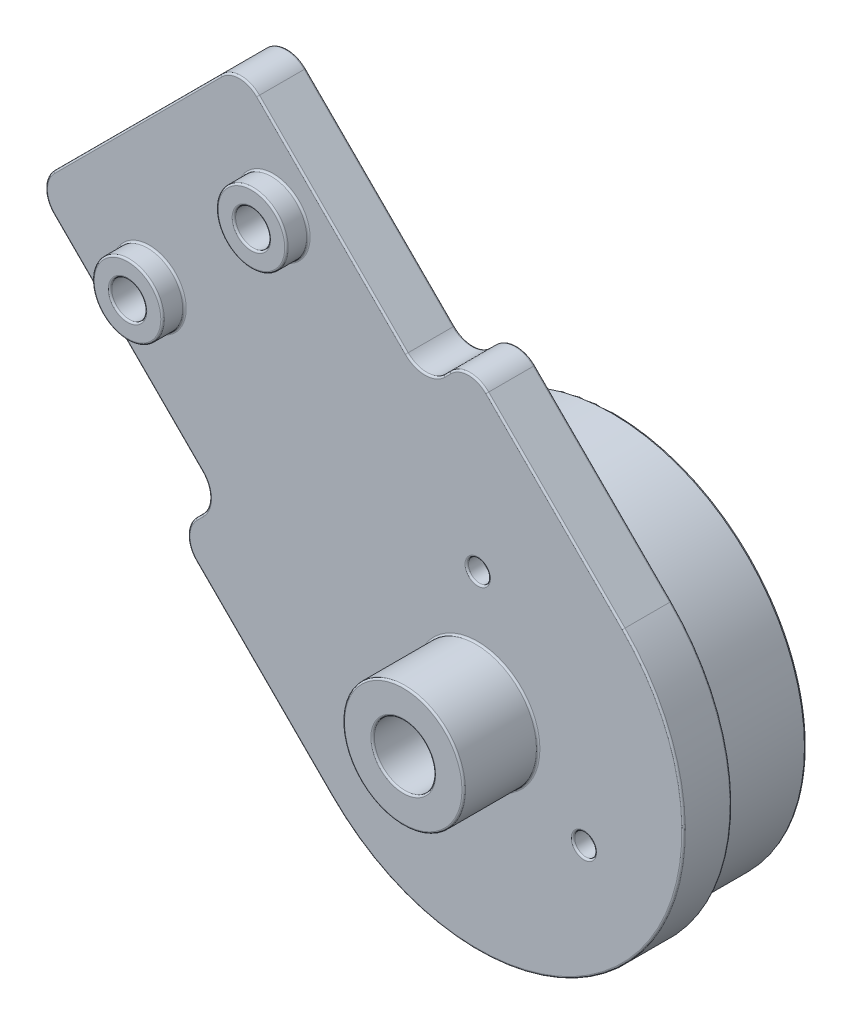
SolidWorks part; units mm, degrees
ref_plane "Front Plane" through (0, 0, 0) normal (0, 0, 1) x (1, 0, 0)
ref_plane "Top Plane" through (0, 0, 0) normal (0, 1, 0) x (1, 0, 0)
ref_plane "Right Plane" through (0, 0, 0) normal (1, 0, 0) x (0, 0, -1)
sketch "Sketch1" plane through (0, 0, 0) normal (0, 0, 1) x (1, 0, 0)
  line L0 (-100, 0) -> (100, 0) construction
  line L1 (-100, 0) -> (0, 100) construction
  line L2 (0, 100) -> (100, 0) construction
  line L3 (0, 0) -> (-50, 50) construction
  line L4 (-40, 60) -> (40, 60) construction
  line L5 (0, 100) -> (0, 60) construction
  line L6 (-56.5165, 43.4835) -> (-40, 60)
  line L7 (-40, 60) -> (40, 60)
  line L8 (40, 60) -> (86.565, 13.435) construction
  line L9 (-49.4454, 36.4124) -> (-35.8579, 50)
  line L10 (-35.8579, 50) -> (35.8579, 50)
  line L11 (35.8579, 50) -> (79.4939, 6.364)
  line L12 (-63.5876, 50.5546) -> (-44.1421, 70)
  line L13 (-44.1421, 70) -> (44.1421, 70)
  line L14 (44.1421, 70) -> (93.636, 20.5061)
  line L15 (-63.5876, 50.5546) -> (-49.4454, 36.4124)
  line L16 (93.636, 20.5061) -> (79.4939, 6.364)
  line L17 (91.1612, 18.0312) -> (104.5962, 4.5962)
  line L18 (81.9688, 8.8388) -> (95.4038, -4.5962)
  line L19 (90.1005, 24.0416) -> (75.9584, 9.8995) construction
  line L20 (6, 70) -> (3.4304, 82.6944)
  line L21 (-6, 70) -> (-3.4304, 82.6944)
  line L22 (40, 60) -> (86.565, 13.435)
  circle A0 centre (-100, 0) radius 20
  circle A1 centre (0, 0) radius 20
  circle A2 centre (100, 0) radius 20
  circle A3 centre (100, 0) radius 10 construction
  circle A4 centre (100, 0) radius 3.5
  arc A5 (95.4038, -4.5962) -> (104.5962, 4.5962) centre (100, 0) ccw
  circle A6 centre (100, 0) radius 6.5 construction
  circle A7 centre (79.4939, 13.435) radius 1
  circle A8 centre (86.565, 20.5061) radius 1
  circle A9 centre (0, 60) radius 1.5
  circle A10 centre (0, 82) radius 1.5
  arc A11 (3.4304, 82.6944) -> (-3.4304, 82.6944) centre (0, 82) ccw
  circle A12 centre (0, 82) radius 3.5 construction
  circle A13 centre (-50, 50) radius 1.5
  point P2 (0, 0)
  dimension "D5" = 40
  dimension "D9" = 20
  dimension "D10" = 7
  dimension "D14" = 2
  dimension "D17" = 3
  dimension "D22" = 3
  dimension "D1" = 200
  dimension "D2" = 90
  dimension "D3" = 90
  dimension "D4" = 80
  dimension "D8" = 27.5
  dimension "D12" = 19
  dimension "D13" = 5
  dimension "D15" = 5
  dimension "D16" = 5
  dimension "D18" = 12
  dimension "D20" = 6
  dimension "D21" = 6
  dimension "D6" = 10
  dimension "D7" = 10
  dimension "D11" = 3
  dimension "D19" = 2
sketch "Sketch2" plane through (0, 0, 0) normal (0, 0, 1) x (1, 0, 0)
  line L0 (-86.565, 13.435) -> (-50, 50) construction
  line L1 (-100, 0) -> (0, 100) construction
  line L2 (-50, 50) -> (-13.435, 13.435) construction
  line L3 (0, 0) -> (-50, 50) construction
  line L4 (-79.4939, 6.364) -> (-50, 35.8579)
  line L5 (-50, 35.8579) -> (-20.5061, 6.364)
  line L6 (-93.636, 20.5061) -> (-50, 64.1421)
  line L7 (-50, 64.1421) -> (-6.364, 20.5061)
  line L8 (-93.636, 20.5061) -> (-50, 64.1421) construction
  line L9 (-79.4939, 6.364) -> (-50, 35.8579) construction
  line L10 (-93.636, 20.5061) -> (-79.4939, 6.364)
  line L11 (-6.364, 20.5061) -> (-20.5061, 6.364)
  line L12 (-104.534, 4.6576) -> (-90.9809, 17.8509)
  line L13 (-95.3424, -4.534) -> (-82.1491, 9.0191)
  line L14 (-18.0312, 8.8388) -> (-4.5962, -4.5962)
  line L15 (-8.8388, 18.0312) -> (4.5962, 4.5962)
  line L16 (-91.8683, 22.2739) -> (-77.7261, 8.1317) construction
  line L17 (-8.1317, 22.2739) -> (-22.2739, 8.1317) construction
  circle A0 centre (-100, 0) radius 3.5
  circle A1 centre (-100, 0) radius 10 construction
  circle A2 centre (0, 0) radius 3.5
  circle A3 centre (0, 0) radius 10 construction
  arc A4 (-4.5962, -4.5962) -> (4.5962, 4.5962) centre (0, 0) ccw
  arc A5 (-104.534, 4.6576) -> (-95.3424, -4.534) centre (-100, 0) ccw
  circle A6 centre (-100, 0) radius 20 construction
  circle A7 centre (-100, 0) radius 6.5 construction
  circle A8 centre (0, 0) radius 6.5 construction
  circle A9 centre (-88.3327, 18.7383) radius 1
  circle A10 centre (-81.2617, 11.6673) radius 1
  circle A11 centre (-18.7383, 11.6673) radius 1
  circle A12 centre (-11.6673, 18.7383) radius 1
  dimension "D1" = 20
  dimension "D2" = 7
  dimension "D8" = 2
  dimension "D6" = 19
  dimension "D7" = 19
  dimension "D9" = 5
  dimension "D10" = 5
  dimension "D11" = 5
  dimension "D12" = 5
  dimension "D13" = 5
  dimension "D14" = 5
  dimension "D3" = 3
  dimension "D4" = 10
  dimension "D5" = 10
sketch "Sketch3" plane through (0, 0, 0) normal (0, 0, 1) x (1, 0, 0)
  line L0 (86.3882, 25.2791) -> (74.7209, 13.6118)
  line L1 (40, 60) -> (86.565, 13.435) construction
  line L2 (90.1005, 24.0416) -> (75.9584, 9.8995) construction
  line L3 (74.7209, 13.6118) -> (85.3275, 3.0052)
  line L4 (85.3275, 3.0052) -> (82.8527, 0.5303)
  line L5 (82.8527, 0.5303) -> (91.6915, -8.3085)
  line L6 (93.636, 20.5061) -> (79.4939, 6.364) construction
  line L7 (100, 0) -> (88.9536, 11.0464) construction
  line L8 (0, 100) -> (100, 0) construction
  line L9 (99.4697, 17.1473) -> (108.3085, 8.3085)
  line L10 (96.9948, 14.6725) -> (99.4697, 17.1473)
  line L11 (86.3882, 25.2791) -> (96.9948, 14.6725)
  circle A0 centre (100, 0) radius 10 construction
  circle A1 centre (100, 0) radius 10
  arc A2 (91.6915, -8.3085) -> (108.3085, 8.3085) centre (100, 0) ccw
  circle A3 centre (100, 0) radius 11.75 construction
  circle A4 centre (79.4939, 13.435) radius 1 construction
  circle A5 centre (86.565, 20.5061) radius 1 construction
  circle A6 centre (79.4939, 13.435) radius 1 construction
  circle A7 centre (86.565, 20.5061) radius 1 construction
  point P7 (80.5546, 19.4454)
  point P29 (0, 0)
  point P30 (0, 0)
  point P31 (0, 0)
  point P32 (0, 0)
  point P33 (0, 0)
  point P34 (0, 0)
  dimension "D2" = 16.5
  dimension "D3" = 12.5
  dimension "D4" = 15
  dimension "D1" = 1.75
extrude "Boss-Extrude1" add sketch "Sketch3" along normal blind 2.75
sketch "Sketch5" plane through (0, 0, 0) normal (0, 0, 1) x (1, 0, 0)
  line L0 (90.6308, 21.0364) -> (78.9636, 9.3692) construction
  line L1 (86.3882, 25.2791) -> (96.9948, 14.6725) construction
  line L2 (74.7209, 13.6118) -> (85.3275, 3.0052) construction
  line L3 (86.3882, 25.2791) -> (74.7209, 13.6118) construction
  circle A0 centre (81.2617, 11.6673) radius 1
  circle A1 centre (88.3327, 18.7383) radius 1
  circle A2 centre (79.4939, 13.435) radius 1 construction
  point P19 (0, 0)
  point P20 (0, 0)
  dimension "D1" = 21.5
extrude "Cut-Extrude1" cut sketch "Sketch5" along normal blind 2.75
sketch "Sketch9" plane through (0, 0, 2.75) normal (0, 0, 1) x (1, 0, 0)
  circle A0 centre (100, 0) radius 10 construction
  circle A1 centre (100, 0) radius 10
extrude "Boss-Extrude3" add sketch "Sketch9" against normal blind 1
sketch "Sketch10" plane through (0, 0, 0) normal (0, 0, -1) x (-1, 0, 0)
  circle A0 centre (-100, 0) radius 11
  circle A1 centre (-100, 0) radius 10
  circle A2 centre (-100, 0) radius 10
  dimension "D1" = 0
  dimension "D2" = 1
extrude "Boss-Extrude4" add sketch "Sketch10" along normal blind 5
fillet "Fillet1" radius 1.5 6 edges at (96.9948, 14.6725, 1.375) (99.4697, 17.1473, 1.375) (82.8527, 0.5303, 1.375) (85.3275, 3.0052, 1.375) (74.7209, 13.6118, 1.375) (86.3882, 25.2791, 1.375)
sketch "Sketch11" plane through (0, 0, 2.75) normal (0, 0, 1) x (1, 0, 0)
  circle A0 centre (81.2617, 11.6673) radius 1 construction
  circle A1 centre (88.3327, 18.7383) radius 1 construction
  circle A2 centre (81.2617, 11.6673) radius 1
  circle A3 centre (88.3327, 18.7383) radius 1
  circle A4 centre (88.3327, 18.7383) radius 2
  circle A5 centre (81.2617, 11.6673) radius 2
  dimension "D1" = 1
extrude "Boss-Extrude5" add sketch "Sketch11" along normal blind 1.25
sketch "Sketch12" plane through (0, 0, 2.75) normal (0, 0, 1) x (1, 0, 0)
  circle A0 centre (100, 0) radius 1.75
  dimension "D1" = 3.5
extrude "Cut-Extrude2" cut sketch "Sketch12" against normal up to surface (1 mm away) up to face at (110, 0, 1.75)
sketch "Sketch13" plane through (0, 0, 2.75) normal (0, 0, 1) x (1, 0, 0)
  circle A0 centre (100, 0) radius 1.75 construction
  circle A1 centre (100, 0) radius 1.75
  circle A2 centre (100, 0) radius 3.45
  dimension "D1" = 6.9
extrude "Boss-Extrude6" add sketch "Sketch13" along normal blind 4.25
sketch "Sketch14" plane through (0, 0, 2.75) normal (0, 0, 1) x (1, 0, 0)
  line L0 (100, 0) -> (100, 7) construction
  circle A0 centre (100, 7) radius 0.625
  circle A1 centre (106.0622, -3.5) radius 0.625
  circle A2 centre (93.9378, -3.5) radius 0.625
  dimension "D1" = 1.25
  dimension "D2" = 7
  dimension "D3" = 3
extrude "Cut-Extrude3" cut sketch "Sketch14" against normal up to surface (1 mm away) up to face at (101.75, 0, 1.75)
fillet "Fillet2" radius 0.1 50 edges at (94.5628, -3.5, 2.75) (94.5628, -3.5, 1.75) (106.6872, -3.5, 2.75) (106.6872, -3.5, 1.75) (100.625, 7, 2.75) (100.625, 7, 1.75) (101.75, 0, 7) (103.45, 0, 2.75) (103.45, 0, 7) (101.75, 0, 1.75) (82.2617, 11.6673, 4) (83.2617, 11.6673, 2.75) (83.2617, 11.6673, 4) (89.3327, 18.7383, 4) (90.3327, 18.7383, 2.75) (90.3327, 18.7383, 4) (90, 0, -5) (89, 0, -5) (110, 0, 1.75) (89.3327, 18.7383, 0) (82.2617, 11.6673, 0) (91.6915, 19.9758, 0) (80.5546, 19.4454, 0) (80.0242, 8.3085, 0) (84.0901, 1.7678, 0) (87.8024, -4.4194, 0) (108.3085, -8.3085, 0) (104.4194, 12.1976, 0) (98.2322, 15.9099, 0) (91.6915, 19.9758, 2.75) (80.5546, 19.4454, 2.75) (80.0242, 8.3085, 2.75) (84.0901, 1.7678, 2.75) (87.8024, -4.4194, 2.75) (108.3085, -8.3085, 2.75) (98.2322, 15.9099, 2.75) (111, 0, 0) (86.3882, 24.6577, 0) (75.3423, 13.6118, 0) (83.474, 0.5303, 0) (99.4697, 16.526, 0) (86.3882, 24.6577, 2.75) (75.3423, 13.6118, 2.75) (83.474, 0.5303, 2.75) (99.4697, 16.526, 2.75) (96.9948, 15.2938, 0) (96.9948, 15.2938, 2.75) (84.7062, 3.0052, 0) (84.7062, 3.0052, 2.75) (104.4194, 12.1976, 2.75)
